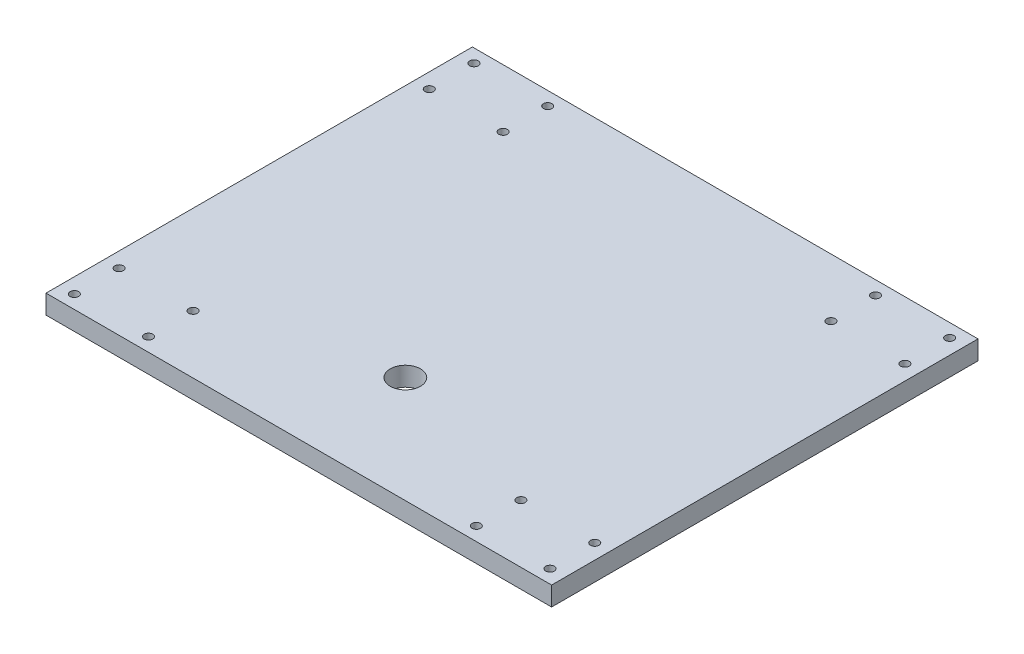
SolidWorks part; units mm, degrees
ref_plane "Front Plane" through (0, 0, 0) normal (0, 0, 1) x (1, 0, 0)
ref_plane "Top Plane" through (0, 0, 0) normal (0, 1, 0) x (1, 0, 0)
ref_plane "Right Plane" through (0, 0, 0) normal (1, 0, 0) x (0, 0, -1)
sketch "Sketch1" plane through (0, 0, 0) normal (0, 1, 0) x (1, 0, 0)
  line L1 (-504, 425) -> (0, 425)
  line L2 (-504, 425) -> (-504, 0)
  line L3 (-504, 0) -> (0, 0)
  line L4 (0, 425) -> (0, 0)
  circle A0 centre (-252, 106.2) radius 15.0812
  dimension "D3" = 30.1625
  dimension "D1" = 504
  dimension "D2" = 425
  dimension "D4" = 252
  dimension "D5" = 106.2
extrude "Boss-Extrude1" add sketch "Sketch1" along normal blind 19
sketch "Sketch2" plane through (0, 19, 0) normal (0, 1, 0) x (1, 0, 0)
  line L5 (-504, 212.5) -> (0, 212.5) construction
  line L6 (-504, 425) -> (-504, 0) construction
  line L7 (0, 0) -> (0, 425) construction
  line L8 (-252, 425) -> (-252, 0) construction
  line L9 (0, 425) -> (-504, 425) construction
  line L10 (-504, 0) -> (0, 0) construction
  circle A0 centre (-88.5994, 57.982) radius 4.25
  circle A1 centre (-14.9394, 57.9115) radius 4.25
  circle A2 centre (-88.5994, 13.532) radius 4.25
  circle A3 centre (-14.9396, 13.337) radius 4.25
  circle A4 centre (-14.9396, 411.663) radius 4.25
  circle A5 centre (-88.5994, 411.468) radius 4.25
  circle A6 centre (-14.9394, 367.0885) radius 4.25
  circle A7 centre (-88.5994, 367.018) radius 4.25
  circle A8 centre (-415.4006, 367.018) radius 4.25
  circle A9 centre (-489.0606, 367.0885) radius 4.25
  circle A10 centre (-415.4006, 411.468) radius 4.25
  circle A11 centre (-489.0604, 411.663) radius 4.25
  circle A12 centre (-489.0604, 13.337) radius 4.25
  circle A13 centre (-415.4006, 13.532) radius 4.25
  circle A14 centre (-489.0606, 57.9115) radius 4.25
  circle A15 centre (-415.4006, 57.982) radius 4.25
  dimension "D3" = 8.5
  dimension "D4" = 8.5
  dimension "D5" = 8.5
  dimension "D6" = 8.5
  dimension "D7" = 73.66
  dimension "D8" = 44.45
  dimension "D9" = 73.66
extrude "Cut-Extrude3" cut sketch "Sketch2" against normal blind 19
